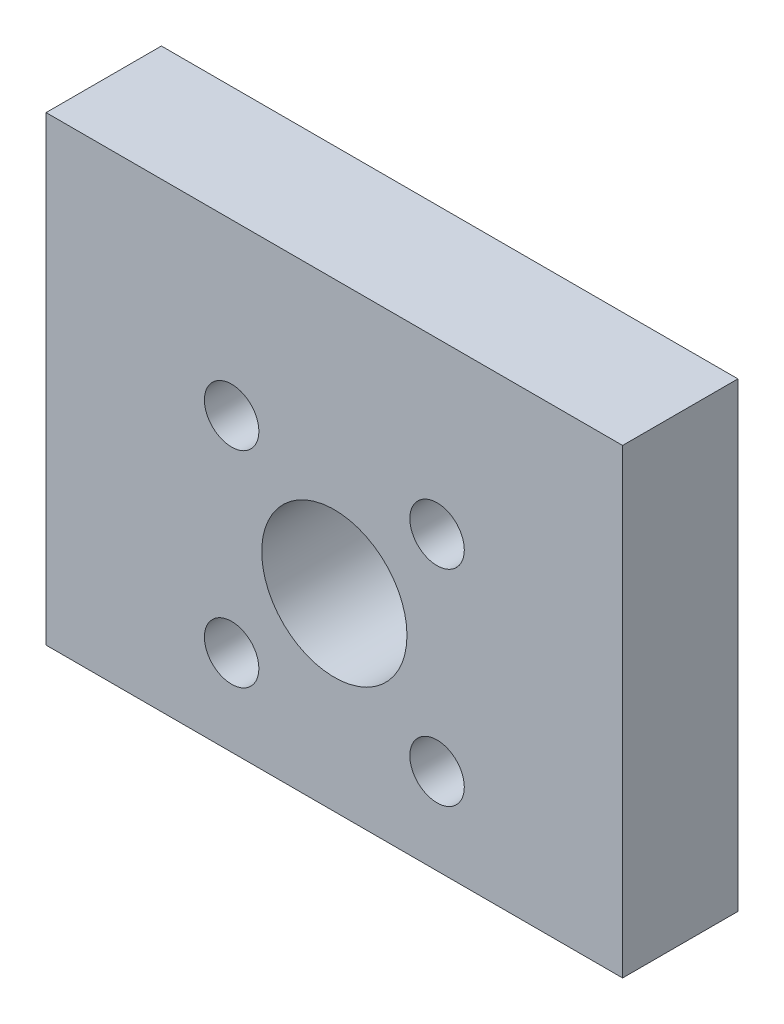
SolidWorks part; units mm, degrees
ref_plane "Front Plane" through (0, 0, 0) normal (0, 0, 1) x (1, 0, 0)
ref_plane "Top Plane" through (0, 0, 0) normal (0, 1, 0) x (1, 0, 0)
ref_plane "Right Plane" through (0, 0, 0) normal (1, 0, 0) x (0, 0, -1)
sketch "front profile" plane through (0, 0, 0) normal (0, 0, 1) x (1, 0, 0)
  line L0 (-15.875, 0) -> (-15.875, 25.4) construction
  line L1 (0, 0) -> (-31.75, 0)
  line L2 (0, 0) -> (0, 25.4)
  line L3 (0, 25.4) -> (-31.75, 25.4)
  line L4 (-31.75, 0) -> (-31.75, 25.4)
  line L5 (0, 10.4) -> (-31.75, 10.4) construction
  line L6 (-15.875, 10.4) -> (-21.5319, 16.0569) construction
  circle A0 centre (-15.875, 10.4) radius 4
  circle A1 centre (-21.5319, 16.0569) radius 1.6012 construction
  dimension "D2" = 8
  dimension "D7" = 3.2025
  dimension "D1" = 25.4
  dimension "D3" = 31.75
  dimension "D5" = 8
  dimension "D4" = 45
  dimension "D6" = 15
extrude "wepon motor moint" add sketch "front profile" along normal blind 6.35 contours A1 | L4 L1 L2 L3 A1 A0
hole_wizard "Ø3.0mm Dowel Hole1" positions "Sketch1" profile "Sketch2" hole size "Ø3.0" standard "ANSI Metric" end condition through all
sketch "Sketch1" plane through (0, 0, 6.35) normal (0, 0, 1) x (1, 0, 0)
  point P0 (-21.5319, 16.0569)
sketch "Sketch2" plane through (-21.5319, 16.0569, 6.35) normal (1, 0, 0) x (0, -1, 0)
  line L0 (0, 0) -> (0, 6.35)
  line L1 (0, 6.35) -> (1.5, 6.35)
  line L2 (1.5, 6.35) -> (1.5, 0)
  line L5 (1.5, 0) -> (0, 0)
  line L11 (0, -6.35) -> (0, 107.95) construction
  dimension "Thru Hole Dia." = 3
  dimension "Thru Hole Depth" = 6.35
pattern_circular "CirPattern1" count 4 over 360 about axis through (-15.875, 10.4, 0) along (0, 0, 1) of "Ø3.0mm Dowel Hole1"
sketch "bolt placement frame" plane through (0, 0, 0) normal (0, 1, 0) x (1, 0, 0)
  line L0 (-25.4, -3.175) -> (-6.35, -3.175) construction
  line L1 (0, -6.35) -> (0, 0) construction
  line L2 (-31.75, -6.35) -> (-31.75, 0) construction
  point P4 (0, -3.175)
  dimension "D1" = 6.35
  dimension "D2" = 6.35
hole_wizard "Ø3.0mm Dowel Hole2" positions "Sketch4" profile "Sketch6" hole size "Ø3.0" standard "ANSI Metric"
sketch "Sketch4" plane through (0, 0, 0) normal (0, -1, 0) x (-1, 0, 0)
  line L0 (25.4, -3.175) -> (6.35, -3.175) construction
  point P0 (6.35, -3.175)
  point P4 (25.4, -3.175)
sketch "Sketch6" plane through (-6.35, 0, 3.175) normal (1, 0, 0) x (0, 0, -1)
  line L0 (0, 0) -> (0, 5.9013)
  line L1 (0, 5.9013) -> (1.5, 5)
  line L2 (1.5, 5) -> (1.5, 0)
  line L5 (1.5, 0) -> (0, 0)
  line L10 (0, 5.9013) -> (-1.5, 5) construction
  line L11 (0, -6.35) -> (0, 107.95) construction
  dimension "Hole Dia." = 3
  dimension "Hole Depth" = 5
  dimension "Drill Angle" = 118
equation "\"width\" = 6in 'side to side 6"
equation "\"height\"= 1.25in'top to bottom from 1.25"
equation "\"length\"=6.25in 'back to front 6.25"
equation "\"side_width\"= 1in"
equation "\"wheel_di\"=1.875in'2.375"
equation "\"wepon_di\" = 1.25in ' milled rectangle must compensate for bolts ~ - .5 1.5"
equation "\"wepon_axle\" = 0.1in ' placement from front .5"
equation "\"frame_bolts\" = 0.125"
equation "\"wheel_base\"= 2.5in"
equation "\"D1@front profile\" = \"height\" - .25in"
